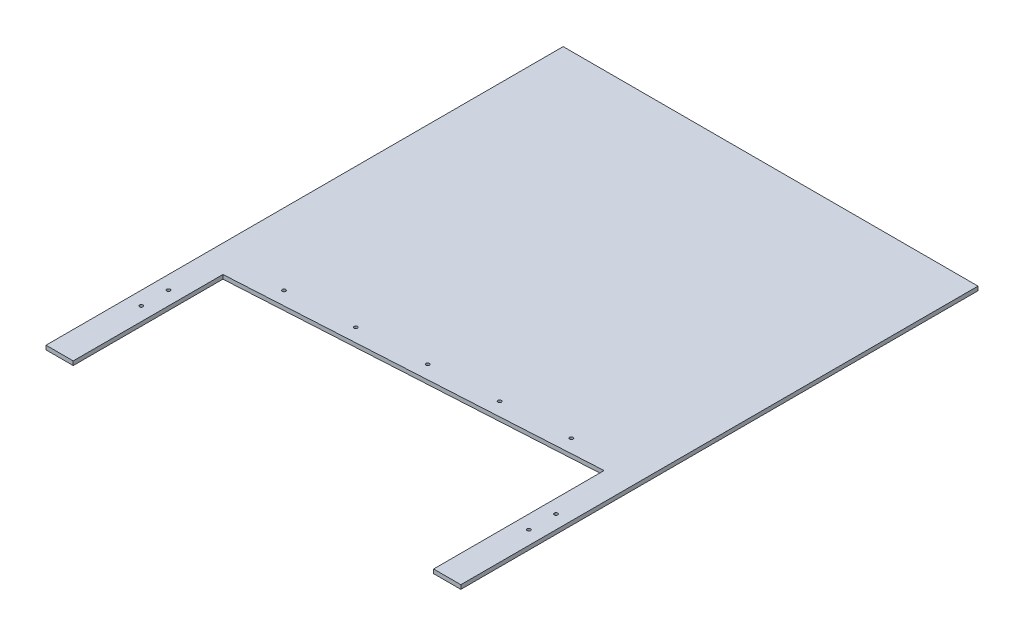
SolidWorks part; units mm, degrees
material "6061 Alloy"
ref_plane "Front Plane" through (0, 0, 0) normal (0, 0, 1) x (1, 0, 0)
ref_plane "Top Plane" through (0, 0, 0) normal (0, 1, 0) x (1, 0, 0)
ref_plane "Right Plane" through (0, 0, 0) normal (1, 0, 0) x (0, 0, -1)
sketch "Sketch1" plane through (0, 0, 0) normal (0, 1, 0) x (1, 0, 0)
  line L0 (-152.4, -135) -> (-152.4, -245)
  line L1 (-152.4, 135) -> (152.4, 135)
  line L2 (-152.4, 135) -> (-152.4, -135)
  line L3 (-152.4, -135) -> (152.4, -135) construction
  line L4 (152.4, 135) -> (152.4, -135)
  line L5 (-152.4, 135) -> (152.4, -135) construction
  line L6 (-152.4, -135) -> (152.4, 135) construction
  line L7 (-152.4, -245) -> (-132.4, -245)
  line L8 (-132.4, -245) -> (-132.4, -135)
  line L9 (-132.4, -135) -> (132.4, -119.7231)
  line L10 (132.4, -119.7231) -> (132.4, -245)
  line L11 (132.4, -245) -> (152.4, -245)
  line L12 (152.4, -245) -> (152.4, -135)
  point P0 (0, 0)
  dimension "D1" = 304.8
  dimension "D2" = 270
  dimension "D3" = 110
  dimension "D4" = 110
  dimension "D5" = 20
  dimension "D6" = 20
  dimension "D7" = 3.302
extrude "Boss-Extrude1" add sketch "Sketch1" along normal blind 3
hole_wizard "Brush Holder Mounting Holes" positions "Sketch3" profile "Sketch2" tap size "M3" standard "ISO"
sketch "Sketch3" plane through (0, 3, 0) normal (0, 1, 0) x (1, 0, 0)
  line L0 (-132.4, -124.5827) -> (132.4, -109.3058) construction
  line L2 (-132.4, -135) -> (132.4, -119.7231) construction
  line L5 (0, -116.9442) -> (0.599, -127.327) construction
  point P0 (0, -116.9442)
  point P2 (-49.917, -119.8241)
  point P4 (-99.834, -122.7039)
  point P6 (49.917, -114.0644)
  point P8 (99.834, -111.1846)
  dimension "D1" = 10.4
  dimension "D2" = 50
  dimension "D3" = 100
  dimension "D4" = 50
  dimension "D5" = 100
sketch "Sketch2" plane through (0, 3, 116.9442) normal (1, 0, 0) x (0, 0, 1)
  line L0 (0, 0) -> (0, 8.2511)
  line L1 (0, 8.2511) -> (1.25, 7.5)
  line L2 (1.25, 7.5) -> (1.25, 0)
  line L5 (1.25, 0) -> (0, 0)
  line L10 (0, 8.2511) -> (-1.25, 7.5) construction
  line L11 (0, -6.35) -> (0, 107.95) construction
  dimension "Tap Drill Dia." = 2.5
  dimension "Tap Drill Depth" = 7.5
  dimension "Drill Angle" = 118
cosmetic thread "Hole Thread1" parameters "D1"=3, "D2"=3
cosmetic thread "Hole Thread2" parameters "D1"=3, "D2"=3
cosmetic thread "Hole Thread3" parameters "D1"=3, "D2"=3
cosmetic thread "Hole Thread4" parameters "D1"=3, "D2"=3
cosmetic thread "Hole Thread5" parameters "D1"=3, "D2"=3
hole_wizard "Omni-Bearing Holes" positions "Sketch5" profile "Sketch4" tap size "M3" standard "ISO"
sketch "Sketch5" plane through (0, 0, 0) normal (0, -1, 0) x (-1, 0, 0)
  line L0 (-152.4, -245) -> (-152.4, 135) construction
  line L1 (152.4, 135) -> (152.4, -245) construction
  line L2 (-152.4, 135) -> (152.4, 135) construction
  point P0 (-142.4, -165)
  point P2 (-142.4, -185)
  point P4 (142.4, -165)
  point P6 (142.4, -185)
  dimension "D1" = 20
  dimension "D2" = 20
  dimension "D3" = 10
  dimension "D4" = 10
  dimension "D5" = 300
  dimension "D6" = 300
sketch "Sketch4" plane through (142.4, 0, 165) normal (1, 0, 0) x (0, 0, -1)
  line L0 (0, 0) -> (0, 8.2511)
  line L1 (0, 8.2511) -> (1.25, 7.5)
  line L2 (1.25, 7.5) -> (1.25, 0)
  line L5 (1.25, 0) -> (0, 0)
  line L10 (0, 8.2511) -> (-1.25, 7.5) construction
  line L11 (0, -6.35) -> (0, 107.95) construction
  dimension "Tap Drill Dia." = 2.5
  dimension "Tap Drill Depth" = 7.5
  dimension "Drill Angle" = 118
cosmetic thread "Hole Thread6" parameters "D1"=3, "D2"=3
cosmetic thread "Hole Thread7" parameters "D1"=3, "D2"=3
cosmetic thread "Hole Thread8" parameters "D1"=3, "D2"=3
cosmetic thread "Hole Thread9" parameters "D1"=3, "D2"=3
equation "\"D7@Sketch1\"=atn( 15/260)"
